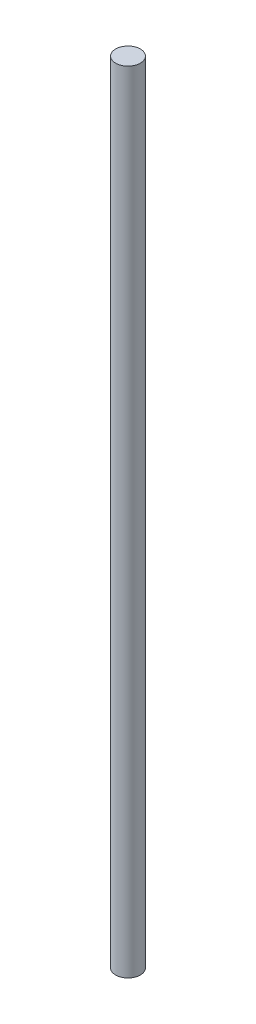
SolidWorks part; units mm, degrees
ref_plane "Front Plane" through (0, 0, 0) normal (0, 0, 1) x (1, 0, 0)
ref_plane "Top Plane" through (0, 0, 0) normal (0, 1, 0) x (1, 0, 0)
ref_plane "Right Plane" through (0, 0, 0) normal (1, 0, 0) x (0, 0, -1)
sketch "Sketch1" plane through (0, 0, 0) normal (0, 1, 0) x (1, 0, 0)
  circle A0 centre (0, 0) radius 3.9688
  dimension "D1" = 7.9375
extrude "Boss-Extrude1" add sketch "Sketch1" along normal blind 254
